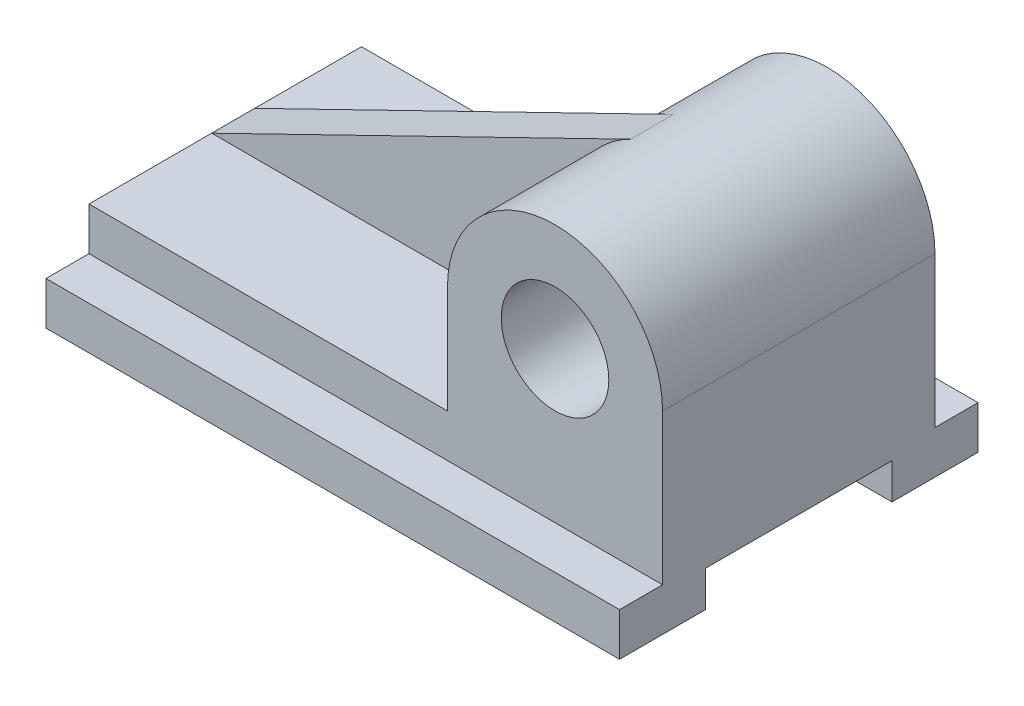
SolidWorks part; units mm, degrees
ref_plane "Front Plane" through (0, 0, 0) normal (0, 0, 1) x (1, 0, 0)
ref_plane "Top Plane" through (0, 0, 0) normal (0, 1, 0) x (1, 0, 0)
ref_plane "Right Plane" through (0, 0, 0) normal (1, 0, 0) x (0, 0, -1)
sketch "Sketch2" plane through (0, 0, 0) normal (1, 0, 0) x (0, 0, -1)
  line L0 (53.7778, 0) -> (53.7778, 12)
  line L1 (53.7778, 12) -> (41.7778, 12)
  line L2 (41.7778, 12) -> (41.7778, 24)
  line L3 (41.7778, 24) -> (-34.2222, 24)
  line L4 (-34.2222, 24) -> (-34.2222, 12)
  line L5 (-34.2222, 12) -> (-46.2222, 12)
  line L6 (-46.2222, 12) -> (-46.2222, 0)
  line L7 (53.7778, 0) -> (29.7778, 0)
  line L8 (29.7778, 0) -> (29.7778, 10)
  line L9 (29.7778, 10) -> (-22.2222, 10)
  line L10 (-22.2222, 10) -> (-22.2222, 0)
  line L11 (-22.2222, 0) -> (-46.2222, 0)
  dimension "D1" = 12
  dimension "D2" = 76
  dimension "D3" = 10
  dimension "D4" = 52
  dimension "D5" = 24
extrude "Boss-Extrude1" add sketch "Sketch2" along normal blind 160
ref_plane "Plane1" through (0, 0, 34.2222) normal (0, 0, 1) x (1, 0, 0)
sketch "Sketch3" plane through (0, 0, 34.2222) normal (0, 0, 1) x (1, 0, 0)
  line L0 (160, 12) -> (160, 54)
  line L1 (100, 54) -> (100, 24)
  line L2 (160, 24) -> (0, 24) construction
  line L3 (100, 24) -> (160, 24)
  arc A0 (160, 54) -> (100, 54) centre (130, 54) ccw
  circle A1 centre (130, 54) radius 15
  dimension "D2" = 30
  dimension "D3" = 30
  dimension "D1" = 42
extrude "Boss-Extrude2" add sketch "Sketch3" against normal blind 76 contours L0 A0 L1 L3 A1
sketch "Sketch4" plane through (0, 0, 0) normal (0, 0, 1) x (1, 0, 0)
  line L0 (116.8539, 80.9663) -> (0, 24)
  line L1 (0, 24) -> (100, 24)
  line L2 (100, 24) -> (100, 54)
  arc A0 (160, 54) -> (100, 54) centre (130, 54) ccw construction
  arc A1 (100, 54) -> (116.8539, 80.9663) centre (130, 54) cw
extrude "Boss-Extrude4" add sketch "Sketch4" against normal blind 12
